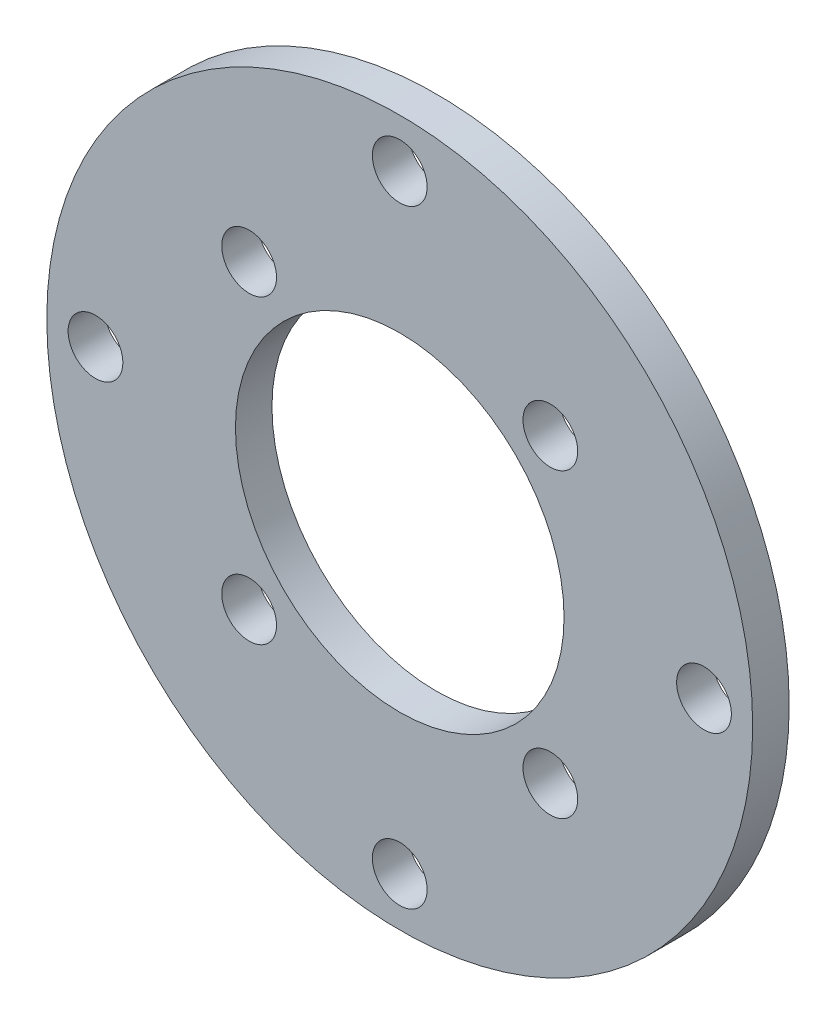
SolidWorks part; units mm, degrees
material "Plain Carbon Steel"
ref_plane "Front Plane" through (0, 0, 0) normal (0, 0, 1) x (1, 0, 0)
ref_plane "Top Plane" through (0, 0, 0) normal (0, 1, 0) x (1, 0, 0)
ref_plane "Right Plane" through (0, 0, 0) normal (1, 0, 0) x (0, 0, -1)
sketch "Sketch1" plane through (0, 0, 0) normal (0, 0, 1) x (1, 0, 0)
  line L0 (-12.3744, 12.3744) -> (0, 0) construction
  line L1 (0, 0) -> (-12.3744, 12.3744) construction
  line L2 (0, 0) -> (12.3744, 12.3744) construction
  line L3 (0, 0) -> (0, 25) construction
  line L4 (0, 0) -> (25, 0) construction
  circle A0 centre (0, 0) radius 29
  circle A1 centre (0, 0) radius 13.5
  circle A2 centre (0, 0) radius 17.5 construction
  circle A3 centre (-12.3744, 12.3744) radius 2.25
  circle A4 centre (12.3744, 12.3744) radius 2.25
  circle A5 centre (12.3744, -12.3744) radius 2.25
  circle A6 centre (-12.3744, -12.3744) radius 2.25
  circle A7 centre (0, 0) radius 25 construction
  circle A8 centre (0, 25) radius 2.25
  circle A9 centre (25, 0) radius 2.25
  circle A10 centre (0, -25) radius 2.25
  circle A11 centre (-25, 0) radius 2.25
  circle A12 centre (0, 0) radius 21 construction
  dimension "D1" = 58
  dimension "D2" = 35
  dimension "D3" = 4.5
  dimension "D5" = 27
  dimension "D6" = 4
  dimension "D8" = 50
  dimension "D11" = 42
  dimension "D4" = 45
  dimension "D7" = 90
  dimension "D10" = 90
  dimension "D9" = 4
extrude "Boss-Extrude1" add sketch "Sketch1" along normal blind 3
